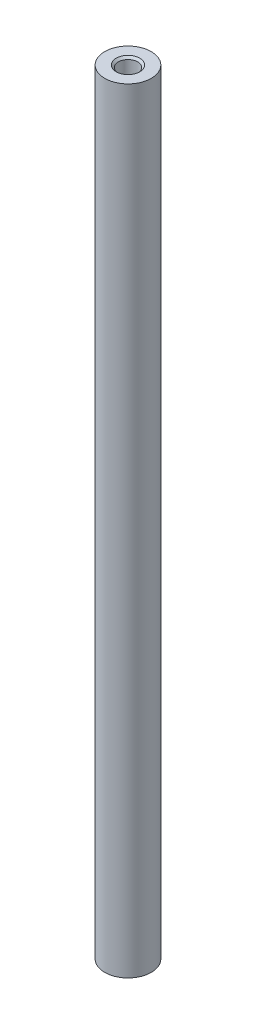
SolidWorks part; units mm, degrees
ref_plane "Front Plane" through (0, 0, 0) normal (0, 0, 1) x (1, 0, 0)
ref_plane "Top Plane" through (0, 0, 0) normal (0, 1, 0) x (1, 0, 0)
ref_plane "Right Plane" through (0, 0, 0) normal (1, 0, 0) x (0, 0, -1)
sketch "Sketch1" plane through (0, 0, 0) normal (0, 1, 0) x (1, 0, 0)
  circle A0 centre (0, 0) radius 3
  dimension "D1" = 6
extrude "Boss-Extrude1" add sketch "Sketch1" along normal blind 100
hole_wizard "M3x0.5 Tapped Hole1" positions "Sketch4" profile "Sketch3" tap size "M3x0.5" standard "ANSI Metric"
sketch "Sketch4" plane through (0, 0, 0) normal (0, -1, 0) x (-1, 0, 0)
  point P0 (0, 0)
sketch "Sketch3" plane through (0, 0, 0) normal (1, 0, 0) x (0, 0, -1)
  line L0 (0, 0) -> (0, 5.7511)
  line L1 (0, 5.7511) -> (1.25, 5)
  line L2 (1.25, 5) -> (1.25, 0.275)
  line L3 (1.25, 0.275) -> (1.525, 0)
  line L5 (1.525, 0) -> (0, 0)
  line L6 (-1.25, 0.275) -> (-1.525, 0) construction
  line L10 (0, 5.7511) -> (-1.25, 5) construction
  line L11 (0, -6.35) -> (0, 107.95) construction
  dimension "Tap Drill Dia." = 2.5
  dimension "Tap Drill Depth" = 5
  dimension "Near C'Sink Dia." = 3.05
  dimension "Near C'Sink Angle" = 90
  dimension "Drill Angle" = 118
cosmetic thread "Hole Thread1" parameters "D1"=5, "D2"=3
ref_plane "Plane1" through (0, 50, 0) normal (0, 1, 0) x (1, 0, 0)
mirror "Mirror1" about plane through (0, 50, 0) normal (0, 1, 0) of "M3x0.5 Tapped Hole1"
